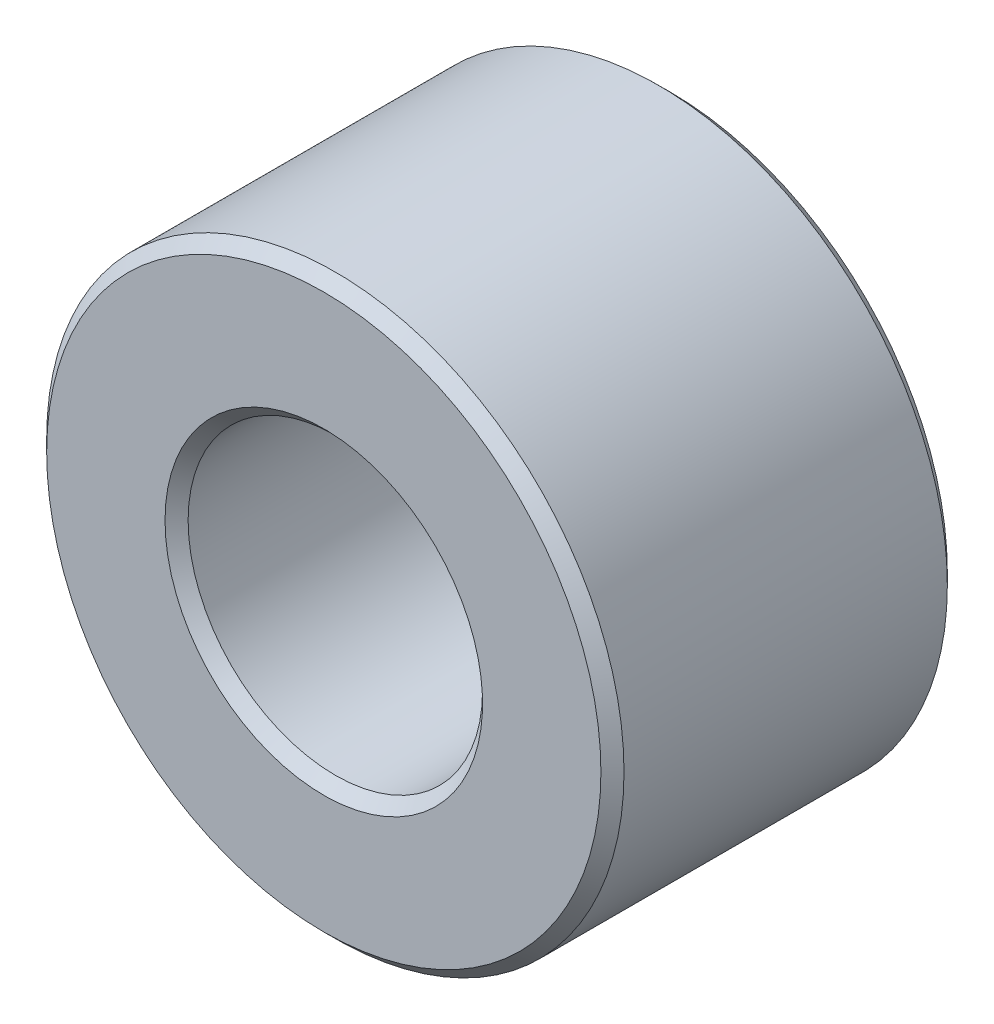
SolidWorks part; units mm, degrees
ref_plane "Front Plane" through (0, 0, 0) normal (0, 0, 1) x (1, 0, 0)
ref_plane "Top Plane" through (0, 0, 0) normal (0, 1, 0) x (1, 0, 0)
ref_plane "Right Plane" through (0, 0, 0) normal (1, 0, 0) x (0, 0, -1)
ref_plane "Plane1" through (0, 0, 0) normal (0, -1, 0) x (1, 0, 0)
sketch "Sketch1" plane through (0, 0, 0) normal (0, -1, 0) x (1, 0, 0)
  line L0 (2.75, 6) -> (2.55, 5.8)
  line L1 (2.55, 5.8) -> (2.55, 0.2)
  line L2 (2.55, 0.2) -> (2.75, 0)
  line L3 (2.75, 0) -> (4.8, 0)
  line L4 (4.8, 0) -> (5, 0.2)
  line L5 (5, 0.2) -> (5, 5.8)
  line L6 (5, 5.8) -> (4.8, 6)
  line L7 (4.8, 6) -> (2.75, 6)
  line L8 (0, 6) -> (0, 0) construction
revolve "Revolve1" add sketch "Sketch1" angle 360 about L8
